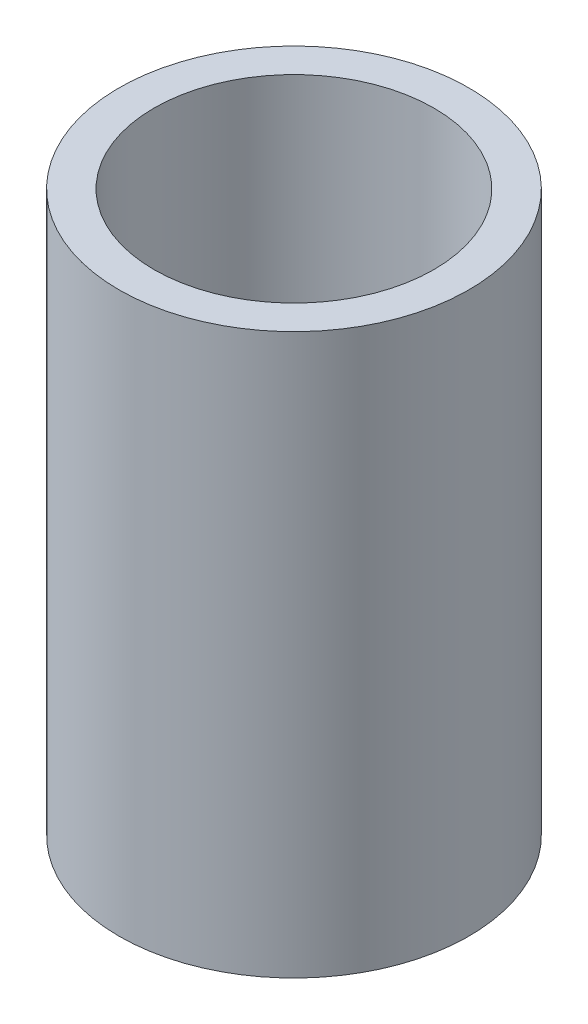
SolidWorks part; units mm, degrees
ref_plane "Front Plane" through (0, 0, 0) normal (0, 0, 1) x (1, 0, 0)
ref_plane "Top Plane" through (0, 0, 0) normal (0, 1, 0) x (1, 0, 0)
ref_plane "Right Plane" through (0, 0, 0) normal (1, 0, 0) x (0, 0, -1)
sketch "Sketch1" plane through (0, 0, 0) normal (0, 1, 0) x (1, 0, 0)
  circle A0 centre (0, 0) radius 7.5
  circle A1 centre (0, 0) radius 6
  dimension "D1" = 15
  dimension "D2" = 12
extrude "Boss-Extrude1" add sketch "Sketch1" along normal blind 24
